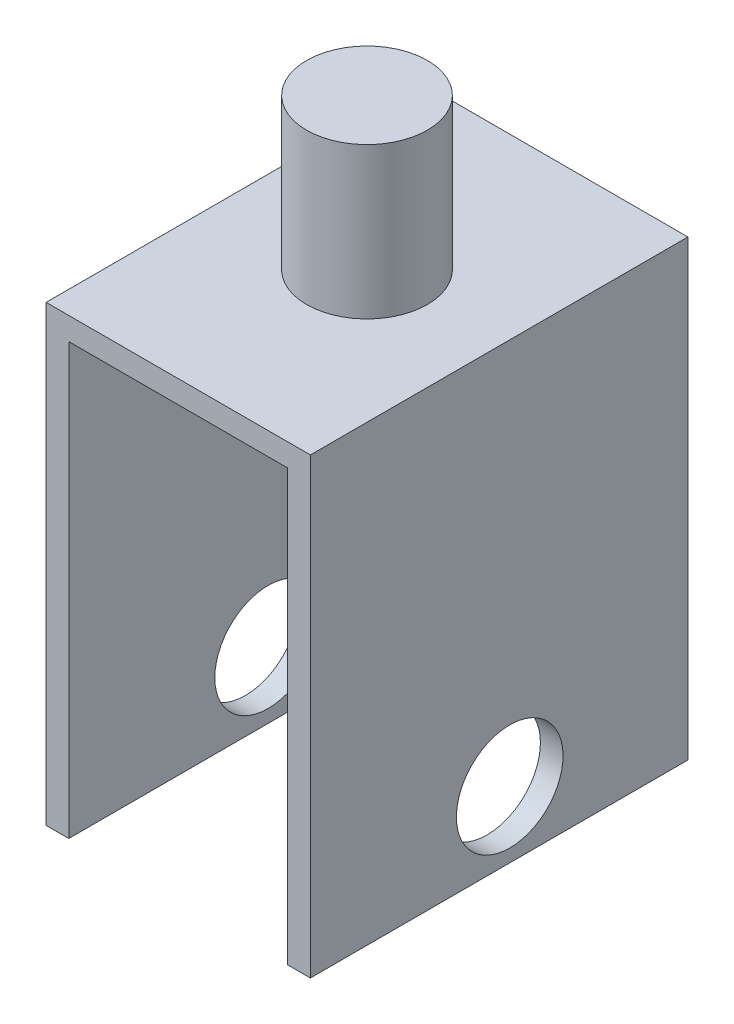
SolidWorks part; units mm, degrees
ref_plane "Front Plane" through (0, 0, 0) normal (0, 0, 1) x (1, 0, 0)
ref_plane "Top Plane" through (0, 0, 0) normal (0, 1, 0) x (1, 0, 0)
ref_plane "Right Plane" through (0, 0, 0) normal (1, 0, 0) x (0, 0, -1)
sketch "Sketch3" plane through (0, 0, 0) normal (0, 0, 1) x (1, 0, 0)
  line L0 (14.5, -30) -> (17.5, -30)
  line L1 (-17.5, 30) -> (17.5, 30)
  line L2 (-17.5, 30) -> (-17.5, -30)
  line L3 (-17.5, -30) -> (-14.5, -30)
  line L4 (17.5, 30) -> (17.5, -30)
  line L5 (-17.5, 30) -> (17.5, -30) construction
  line L6 (-17.5, -30) -> (17.5, 30) construction
  line L8 (-14.5, -30) -> (-14.5, 27)
  line L9 (-14.5, 27) -> (14.5, 27)
  line L10 (14.5, -30) -> (14.5, 27)
  point P0 (0, 0)
  dimension "D3" = 3
  dimension "D1" = 35
  dimension "D2" = 60
  dimension "D4" = 3
  dimension "D5" = 3
extrude "Boss-Extrude2" add sketch "Sketch3" along normal mid plane 50
sketch "Sketch4" plane through (0, 30, 0) normal (0, 1, 0) x (1, 0, 0)
  circle A0 centre (0, 0) radius 8
  dimension "D1" = 16
extrude "Boss-Extrude3" add sketch "Sketch4" along normal blind 20
sketch "Sketch5" plane through (-17.5, 0, 0) normal (-1, 0, 0) x (0, 0, 1)
  circle A0 centre (-1.4033, -21.2315) radius 7.0615
extrude "Cut-Extrude2" cut sketch "Sketch5" against normal through all
